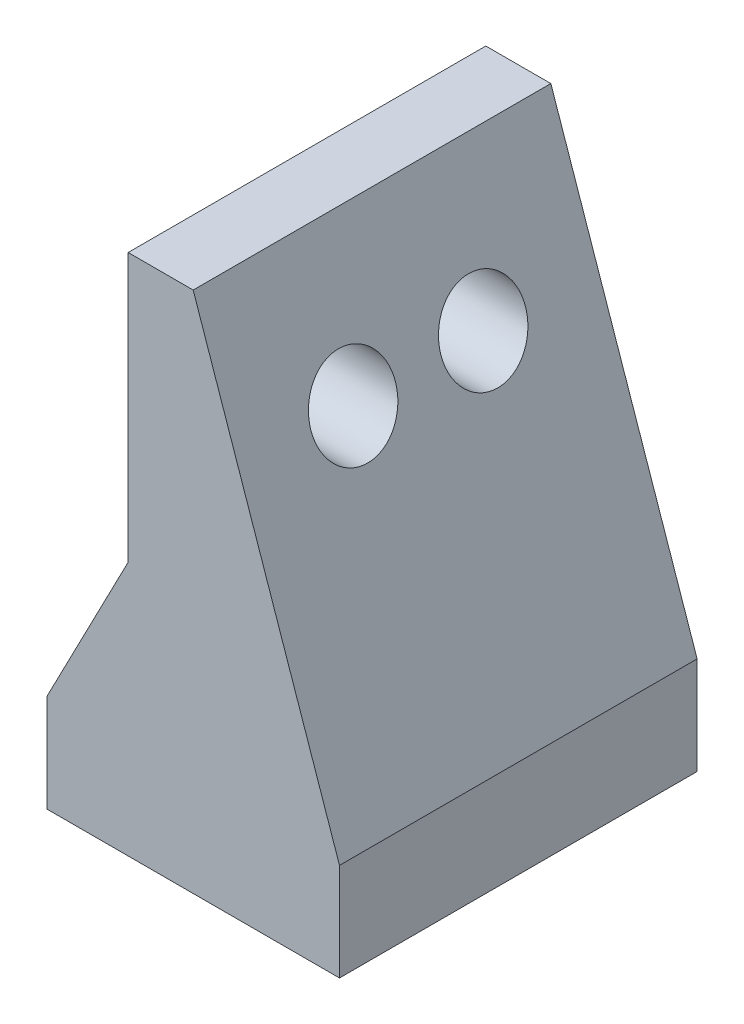
SolidWorks part; units mm, degrees
ref_plane "Front Plane" through (0, 0, 0) normal (0, 0, 1) x (1, 0, 0)
ref_plane "Top Plane" through (0, 0, 0) normal (0, 1, 0) x (1, 0, 0)
ref_plane "Right Plane" through (0, 0, 0) normal (1, 0, 0) x (0, 0, -1)
sketch "Sketch1" plane through (0, 0, 0) normal (0, 0, 1) x (1, 0, 0)
  line L0 (0, 0) -> (0, 6)
  line L1 (5, 15.65) -> (5, 32.15)
  line L2 (0, 6) -> (5, 15.65)
  line L3 (5, 32.15) -> (9, 32.15)
  line L4 (9, 32.15) -> (18, 6)
  line L5 (18, 6) -> (18, 0)
  line L6 (18, 0) -> (0, 0)
  line L7 (5, 23.9) -> (11.8394, 23.9) construction
  dimension "D1" = 16.5
  dimension "D2" = 23.9
  dimension "D3" = 18
  dimension "D4" = 5
  dimension "D5" = 6
  dimension "D6" = 4
extrude "Boss-Extrude1" add sketch "Sketch1" along normal blind 22
sketch "Sketch2" plane through (5, 0, 0) normal (-1, 0, 0) x (0, 0, 1)
  line L0 (0, 23.9) -> (7, 23.9) construction
  line L1 (0, 32.15) -> (0, 15.65) construction
  line L2 (7, 23.9) -> (15, 23.9) construction
  line L3 (15, 23.9) -> (22, 23.9) construction
  line L4 (22, 32.15) -> (22, 15.65) construction
  circle A0 centre (7, 23.9) radius 2.6
  circle A1 centre (15, 23.9) radius 2.6
  dimension "D2" = 5.2
  dimension "D1" = 8
extrude "Cut-Extrude1" cut sketch "Sketch2" against normal through all
sketch "Sketch3" plane through (0, 0, 0) normal (0, -1, 0) x (1, 0, 0)
  line L0 (13, 11) -> (18, 11) construction
  line L1 (18, 22) -> (18, 0) construction
  line L2 (0, 22) -> (0, 0) construction
  line L3 (0, 0) -> (18, 0) construction
  line L5 (0, 22) -> (18, 22) construction
  circle A0 centre (5, 17) radius 2.6
  circle A1 centre (13, 11) radius 2.6
  circle A2 centre (5, 5) radius 2.6
  dimension "D1" = 5.2
  dimension "D2" = 5
  dimension "D3" = 5
  dimension "D4" = 5
  dimension "D5" = 5
extrude "Cut-Extrude2" cut sketch "Sketch3" against normal blind 6
chamfer "Chamfer1" distance 1 angle 45 5 edges at (15.6, 0, 11) (7.6, 0, 17) (7.6, 0, 5) (5, 23.9, 17.6) (5, 23.9, 9.6)
